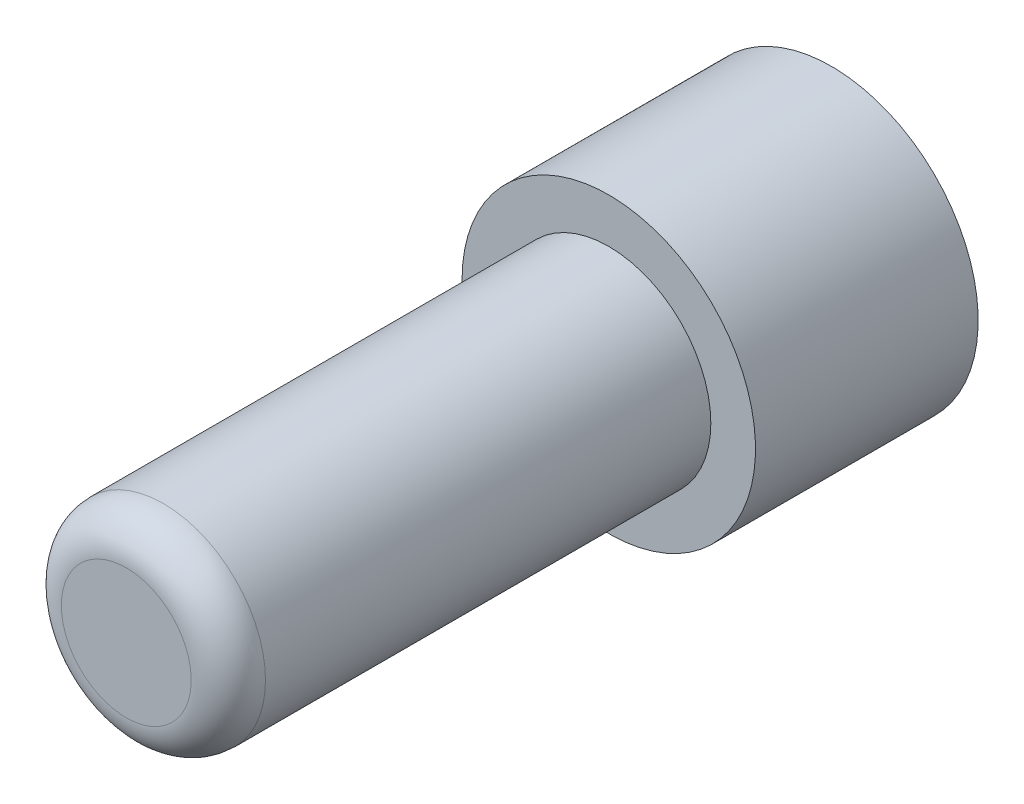
SolidWorks part; units mm, degrees
ref_plane "Front Plane" through (0, 0, 0) normal (0, 0, 1) x (1, 0, 0)
ref_plane "Top Plane" through (0, 0, 0) normal (0, 1, 0) x (1, 0, 0)
ref_plane "Right Plane" through (0, 0, 0) normal (1, 0, 0) x (0, 0, -1)
sketch "Sketch1" plane through (0, 0, 255.7071) normal (0, 0, -1) x (-1, 0, 0)
  circle A0 centre (-95.8626, 210.0631) radius 2.75
  dimension "D1" = 5.5
extrude "Boss-Extrude1" add sketch "Sketch1" along normal blind 5 and the other way blind 8
sketch "Sketch2" plane through (0, 0, 250.7071) normal (0, 0, -1) x (-1, 0, 0)
  circle A0 centre (-95.8626, 210.0631) radius 3.9528
extrude "Boss-Extrude2" add sketch "Sketch2" along normal blind 4
sketch "Sketch3" plane through (0, 0, 246.7071) normal (0, 0, -1) x (-1, 0, 0)
  circle A0 centre (-95.8626, 210.0631) radius 3.9528
  circle A1 centre (-95.8626, 210.0631) radius 2
  dimension "D1" = 4
extrude "Boss-Extrude3" add sketch "Sketch3" along normal blind 2
fillet "Fillet1" radius 1 1 edges at (93.1126, 210.0631, 263.7071)
